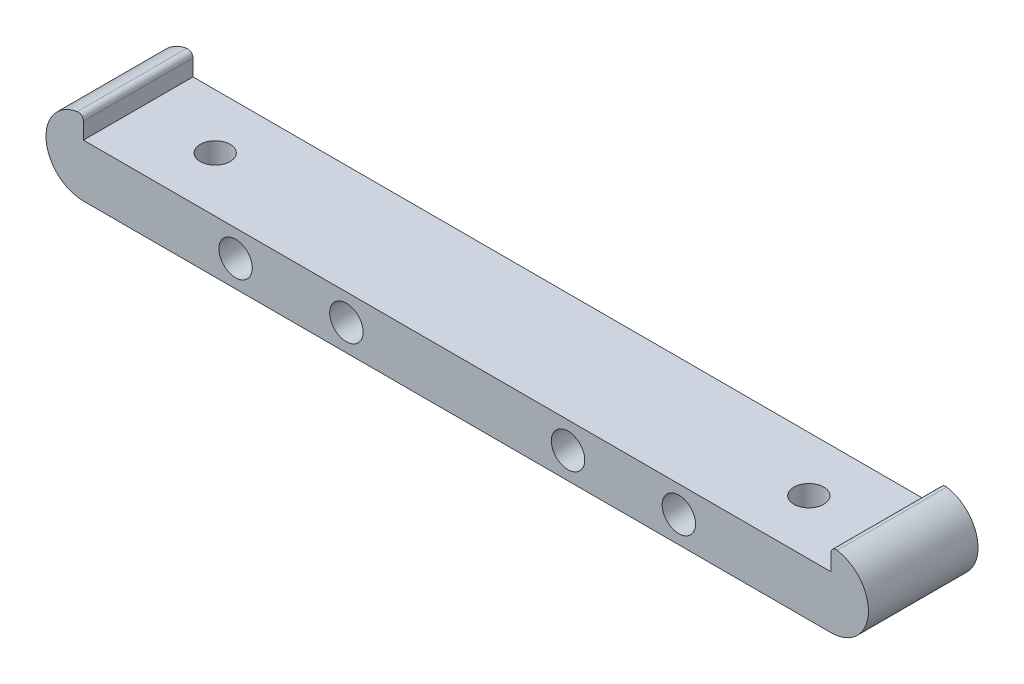
SolidWorks part; units mm, degrees
ref_plane "Front Plane" through (0, 0, 0) normal (0, 0, 1) x (1, 0, 0)
ref_plane "Top Plane" through (0, 0, 0) normal (0, 1, 0) x (1, 0, 0)
ref_plane "Right Plane" through (0, 0, 0) normal (1, 0, 0) x (0, 0, -1)
sketch "Sketch1" plane through (0, 0, 0) normal (0, 0, 1) x (1, 0, 0)
  line L0 (53.975, 7.62) -> (53.975, 0) construction
  line L1 (0, 7.62) -> (107.95, 7.62)
  line L2 (0, 7.62) -> (0, 0) construction
  line L3 (0, 0) -> (107.95, 0) construction
  line L4 (107.95, 7.62) -> (107.95, 0) construction
  line L6 (0, 0) -> (107.95, 0)
  line L7 (0, 10.8204) -> (0, 7.62)
  line L8 (0, 3.81) -> (107.95, 3.81) construction
  line L9 (21.971, 3.81) -> (37.973, 3.81) construction
  line L10 (37.973, 3.81) -> (69.977, 3.81) construction
  line L11 (69.977, 3.81) -> (85.979, 3.81) construction
  line L12 (107.95, 10.8204) -> (107.95, 7.62)
  circle A5 centre (21.971, 3.81) radius 2.413
  circle A6 centre (37.973, 3.81) radius 2.413
  circle A7 centre (69.977, 3.81) radius 2.413
  circle A8 centre (85.979, 3.81) radius 2.413
  arc A9 (0, 10.8204) -> (0, 0) centre (0, 5.4102) ccw
  arc A10 (107.95, 10.8204) -> (107.95, 0) centre (107.95, 5.4102) cw
  point P0 (53.975, 3.81)
  point P19 (77.978, 3.81)
  point P24 (29.972, 3.81)
  dimension "D3" = 3.2004
  dimension "D4" = 16.002
  dimension "D5" = 4.826
  dimension "D1" = 107.95
  dimension "D2" = 7.62
  dimension "D6" = 48.006
extrude "Boss-Extrude1" add sketch "Sketch1" along normal blind 15.8242
sketch "Sketch3" plane through (0, 7.62, 0) normal (0, 1, 0) x (1, 0, 0)
  line L0 (96.8375, -7.9121) -> (11.1125, -7.9121) construction
  line L1 (53.975, -15.8242) -> (53.975, 0) construction
  line L2 (107.95, -15.8242) -> (0, -15.8242) construction
  line L3 (107.95, 0) -> (0, 0) construction
  circle A0 centre (96.8375, -7.9121) radius 2.159
  circle A2 centre (11.1125, -7.9121) radius 2.159
  point P8 (53.975, -7.9121)
  dimension "D1" = 4.318
  dimension "D2" = 85.725
extrude "Cut-Extrude1" cut sketch "Sketch3" against normal up to surface (7.62 mm away) up to face at (53.975, 0, 7.9121)
fillet "Fillet1" radius 0.762 2 edges at (0, 10.8204, 7.9121) (107.95, 10.8204, 7.9121)
